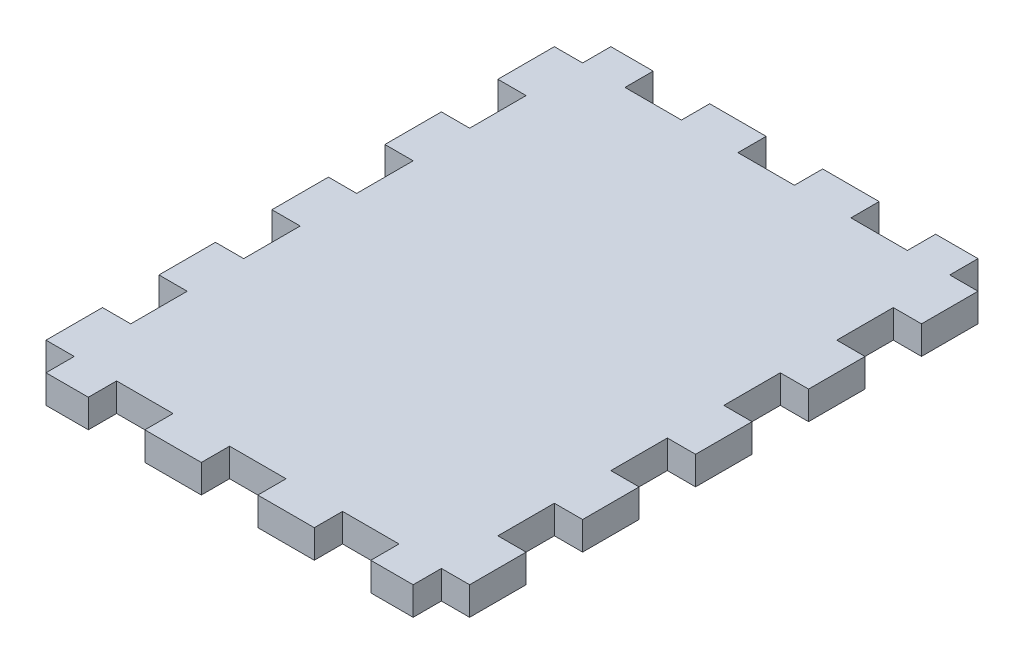
SolidWorks part; units mm, degrees
material "Pine"
ref_plane "Front Plane" through (0, 0, 0) normal (0, 0, 1) x (1, 0, 0)
ref_plane "Top Plane" through (0, 0, 0) normal (0, 1, 0) x (1, 0, 0)
ref_plane "Right Plane" through (0, 0, 0) normal (1, 0, 0) x (0, 0, -1)
sketch "Sketch1" plane through (0, 0, 0) normal (0, 1, 0) x (1, 0, 0)
  line L1 (0, 0) -> (95.25, 0)
  line L2 (0, 0) -> (0, 127)
  line L3 (0, 127) -> (95.25, 127)
  line L4 (95.25, 0) -> (95.25, 127)
  dimension "D1" = 95.25
  dimension "D2" = 127
extrude "Boss-Extrude1" add sketch "Sketch1" along normal blind 6.35 contours L2 L3 L4 L1
sketch "Sketch2" plane through (0, 6.35, 0) normal (0, 1, 0) x (1, 0, 0)
  line L0 (0, 0) -> (0, 127) construction
  line L1 (0, 120.65) -> (6.35, 120.65)
  line L2 (0, 120.65) -> (0, 133.35)
  line L3 (0, 133.35) -> (6.35, 133.35)
  line L4 (6.35, 120.65) -> (6.35, 133.35)
  line L5 (0, 127) -> (95.25, 127) construction
  line L6 (95.25, 0) -> (95.25, 127) construction
  line L7 (95.25, 120.65) -> (88.9, 120.65)
  line L8 (95.25, 120.65) -> (95.25, 133.35)
  line L9 (95.25, 133.35) -> (88.9, 133.35)
  line L10 (88.9, 120.65) -> (88.9, 133.35)
  line L11 (0, 0) -> (95.25, 0) construction
  line L12 (0, 6.35) -> (6.35, 6.35)
  line L13 (0, 6.35) -> (0, 0)
  line L14 (0, 0) -> (6.35, 0)
  line L15 (6.35, 6.35) -> (6.35, 0)
  line L17 (95.25, 6.35) -> (88.9, 6.35)
  line L18 (95.25, 6.35) -> (95.25, 0)
  line L19 (95.25, 0) -> (88.9, 0)
  line L20 (88.9, 6.35) -> (88.9, 0)
  dimension "D1" = 12.7
  dimension "D2" = 6.35
  dimension "D3" = 6.35
extrude "Cut-Extrude1" cut sketch "Sketch2" against normal through all
pattern_linear "LPattern1" count 5 spacing 25.4 along (0, 0, 1) of "Cut-Extrude1"
sketch "Sketch4" plane through (0, 6.35, 0) normal (0, 1, 0) x (1, 0, 0)
  line L0 (6.35, 127) -> (88.9, 127) construction
  line L1 (41.275, 127) -> (53.975, 127)
  line L2 (41.275, 127) -> (41.275, 120.65)
  line L3 (41.275, 120.65) -> (53.975, 120.65)
  line L4 (53.975, 127) -> (53.975, 120.65)
  line L5 (6.35, 0) -> (88.9, 0) construction
  line L6 (41.275, 6.35) -> (53.975, 6.35)
  line L7 (41.275, 6.35) -> (41.275, 0)
  line L8 (41.275, 0) -> (53.975, 0)
  line L9 (53.975, 6.35) -> (53.975, 0)
  point P6 (47.625, 127)
  dimension "D1" = 6.35
  dimension "D2" = 12.7
extrude "Cut-Extrude3" cut sketch "Sketch4" against normal through all contours L3 L4 L1 L2 | L6 L9 L8 L7
pattern_linear "LPattern2" count 2 spacing 25.4 along (-1, 0, 0) count 2 spacing 25.4 along (1, 0, 0) of "Cut-Extrude3"
